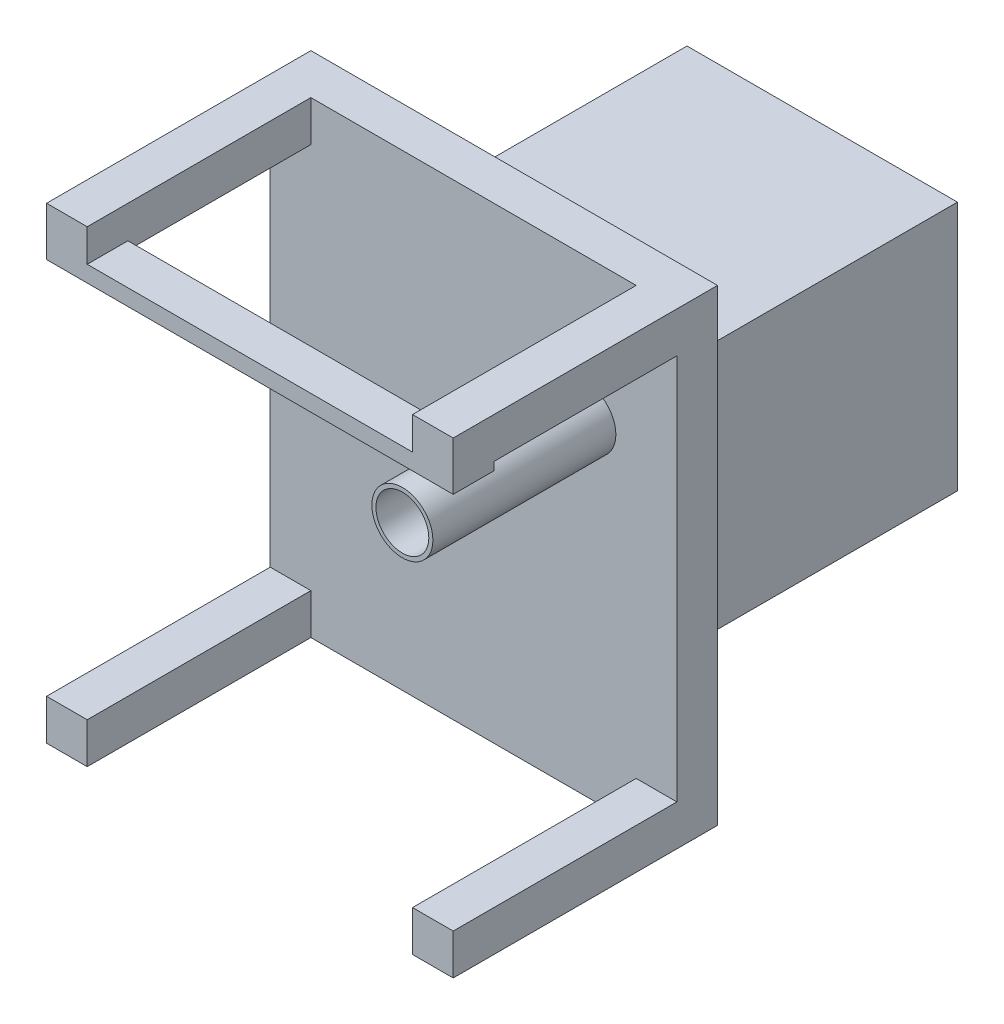
SolidWorks part; units mm, degrees
ref_plane "Plan de face" through (0, 0, 0) normal (0, 0, 1) x (1, 0, 0)
ref_plane "Plan de dessus" through (0, 0, 0) normal (0, 1, 0) x (1, 0, 0)
ref_plane "Plan de droite" through (0, 0, 0) normal (1, 0, 0) x (0, 0, -1)
sketch "Esquisse1" plane through (0, 0, 0) normal (0, 0, 1) x (1, 0, 0)
  line L1 (0, 0) -> (100, 0)
  line L2 (0, 0) -> (0, 115)
  line L3 (0, 115) -> (100, 115)
  line L4 (100, 0) -> (100, 115)
  dimension "D1" = 115
  dimension "D2" = 100
extrude "Boss.-Extru.2" add sketch "Esquisse1" along normal blind 10 contours L2 L1 L4 L3
sketch "Esquisse2" plane through (0, 0, 10) normal (0, 0, 1) x (1, 0, 0)
  line L3 (0, 115) -> (10, 115)
  line L4 (0, 115) -> (0, 105)
  line L5 (0, 105) -> (10, 105)
  line L6 (10, 115) -> (10, 105)
  dimension "D1" = 10
  dimension "D2" = 10
extrude "Boss.-Extru.8" add sketch "Esquisse2" along normal blind 55 contours L4 L3 L6 L5
sketch "Esquisse9" plane through (0, 0, 10) normal (0, 0, 1) x (1, 0, 0)
  line L1 (100, 115) -> (90, 115)
  line L2 (100, 115) -> (100, 105)
  line L3 (100, 105) -> (90, 105)
  line L4 (90, 115) -> (90, 105)
  dimension "D1" = 10
  dimension "D2" = 10
extrude "Boss.-Extru.9" add sketch "Esquisse9" along normal blind 55
sketch "Esquisse10" plane through (0, 0, 10) normal (0, 0, 1) x (1, 0, 0)
  line L1 (0, 0) -> (10, 0)
  line L2 (0, 0) -> (0, 10)
  line L3 (0, 10) -> (10, 10)
  line L4 (10, 0) -> (10, 10)
  dimension "D1" = 10
  dimension "D2" = 10
extrude "Boss.-Extru.10" add sketch "Esquisse10" along normal blind 55
sketch "Esquisse11" plane through (0, 0, 10) normal (0, 0, 1) x (1, 0, 0)
  line L1 (100, 0) -> (90, 0)
  line L2 (100, 0) -> (100, 10)
  line L3 (100, 10) -> (90, 10)
  line L4 (90, 0) -> (90, 10)
  dimension "D1" = 10
  dimension "D2" = 10
extrude "Boss.-Extru.11" add sketch "Esquisse11" along normal blind 55
sketch "Esquisse14" plane through (0, 105, 0) normal (0, -1, 0) x (1, 0, 0)
  line L0 (0, 65) -> (0, 10) construction
  line L1 (100, 65) -> (0, 65)
  line L2 (100, 65) -> (100, 55)
  line L3 (100, 55) -> (0, 55)
  line L4 (0, 65) -> (0, 55)
  dimension "D1" = 10
extrude "Boss.-Extru.12" add sketch "Esquisse14" along normal blind 2
sketch "Esquisse15" plane through (0, 105, 0) normal (0, 1, 0) x (1, 0, 0)
  line L1 (10, -55) -> (90, -55)
  line L2 (10, -55) -> (10, -65)
  line L3 (10, -65) -> (90, -65)
  line L4 (90, -55) -> (90, -65)
extrude "Boss.-Extru.13" add sketch "Esquisse15" along normal blind 2
sketch "Esquisse16" plane through (0, 0, 10) normal (0, 0, 1) x (1, 0, 0)
  line L3 (25.6901, 80.7385) -> (100, 80.7385) construction
  line L4 (100, 10) -> (100, 105) construction
  line L5 (100, 80.7385) -> (85, 80.7385) construction
  line L6 (85, 80.7385) -> (77.5, 80.7385) construction
  circle A1 centre (77.5, 80.7385) radius 7.5
  dimension "D3" = 15
  dimension "D4" = 7.5
extrude "Boss.-Extru.16" add sketch "Esquisse16" along normal blind 45 contours A1
sketch "Esquisse17" plane through (0, 0, 55) normal (0, 0, 1) x (1, 0, 0)
  circle A0 centre (77.5, 80.7385) radius 6.5
extrude "Enlèv. mat.-Extru.1" cut sketch "Esquisse17" against normal blind 59
sketch "Esquisse18" plane through (0, 0, 0) normal (0, 0, -1) x (-1, 0, 0)
  line L0 (-77.5, 87.2385) -> (-27.5, 87.2385)
  line L1 (-84, 80.7385) -> (-84, 30.7385)
  line L2 (-84, 30.7385) -> (-27.5, 30.7385)
  line L3 (-27.5, 30.7385) -> (-27.5, 87.2385)
  line L5 (-27.5, 87.2385) -> (-22.5, 87.2385)
  line L6 (-27.5, 87.2385) -> (-27.5, 30.7385)
  line L7 (-27.5, 30.7385) -> (-22.5, 30.7385)
  line L8 (-22.5, 87.2385) -> (-22.5, 30.7385)
  circle A0 centre (-77.5, 80.7385) radius 6.5 construction
  dimension "D1" = 50
  dimension "D2" = 50
  dimension "D3" = 5
extrude "Boss.-Extru.17" add sketch "Esquisse18" along normal blind 70 contours L8 L5 L3 L7
sketch "Esquisse19" plane through (0, 0, 0) normal (0, 0, -1) x (-1, 0, 0)
  line L1 (-27.5, 30.7385) -> (-84, 30.7385)
  line L2 (-27.5, 30.7385) -> (-27.5, 35.7385)
  line L3 (-27.5, 35.7385) -> (-84, 35.7385)
  line L4 (-84, 30.7385) -> (-84, 35.7385)
  dimension "D1" = 5
extrude "Boss.-Extru.18" add sketch "Esquisse19" along normal blind 70
sketch "Esquisse21" plane through (0, 0, 0) normal (0, 0, -1) x (-1, 0, 0)
  line L1 (-84, 30.7385) -> (-89, 30.7385)
  line L2 (-84, 30.7385) -> (-84, 87.2385)
  line L3 (-84, 87.2385) -> (-89, 87.2385)
  line L4 (-89, 30.7385) -> (-89, 87.2385)
  dimension "D1" = 5
extrude "Boss.-Extru.19" add sketch "Esquisse21" along normal blind 70
sketch "Esquisse22" plane through (0, 0, 0) normal (0, 0, -1) x (-1, 0, 0)
  line L1 (-22.5, 87.2385) -> (-89, 87.2385)
  line L2 (-22.5, 87.2385) -> (-22.5, 92.2385)
  line L3 (-22.5, 92.2385) -> (-89, 92.2385)
  line L4 (-89, 87.2385) -> (-89, 92.2385)
  dimension "D1" = 5
extrude "Boss.-Extru.20" add sketch "Esquisse22" along normal blind 70
sketch "Esquisse25" plane through (27.5, 0, 0) normal (1, 0, 0) x (0, 0, -1)
  line L0 (0, 87.2385) -> (50, 87.2385) construction
  line L1 (70, 87.2385) -> (0, 87.2385) construction
  line L2 (0, 35.7385) -> (50, 35.7385) construction
  line L3 (70, 35.7385) -> (0, 35.7385) construction
  dimension "D1" = 50
  dimension "D2" = 50
sketch "Esquisse26" plane through (0, 0, -70) normal (0, 0, -1) x (-1, 0, 0)
  line L0 (-27.5, 87.2385) -> (-84, 35.7385)
  line L1 (-84, 35.7385) -> (-27.5, 35.7385)
  line L2 (-27.5, 35.7385) -> (-27.5, 87.2385)
extrude "Boss.-Extru.21" add sketch "Esquisse26" against normal up to surface (70 mm away) up to face at (58.5308, 63.7692, 0)
sketch "Esquisse23" plane through (0, 0, -70) normal (0, 0, -1) x (-1, 0, 0)
  line L0 (-27.5, 87.2385) -> (-84, 35.7385)
  line L1 (-84, 35.7385) -> (-27.5, 35.7385)
  line L2 (-27.5, 35.7385) -> (-27.5, 87.2385)
extrude "Enlèv. mat.-Extru.2" cut sketch "Esquisse23" against normal blind 70
sketch "Esquisse24" plane through (0, 87.2385, 0) normal (0, -1, 0) x (1, 0, 0)
  line L0 (27.5, -50) -> (71.5, 0)
  line L1 (77.5, 0) -> (27.5, 0) construction
  line L2 (71.5, 0) -> (27.5, 0)
  line L3 (27.5, 0) -> (27.5, -50)
  dimension "D1" = 44
  dimension "D2" = 50
extrude "Boss.-Extru.26" add sketch "Esquisse24" along normal up to next
sketch "Esquisse29" plane through (84, 0, 0) normal (-1, 0, 0) x (0, 0, 1)
  line L0 (0, 35.7385) -> (-50, 35.7385)
  line L1 (-70, 35.7385) -> (0, 35.7385) construction
  line L2 (-50, 35.7385) -> (0, 74.7385)
  line L3 (0, 35.7385) -> (0, 80.7385) construction
  line L4 (0, 74.7385) -> (0, 35.7385)
  dimension "D1" = 39
  dimension "D2" = 50
extrude "Boss.-Extru.28" add sketch "Esquisse29" along normal up to next
